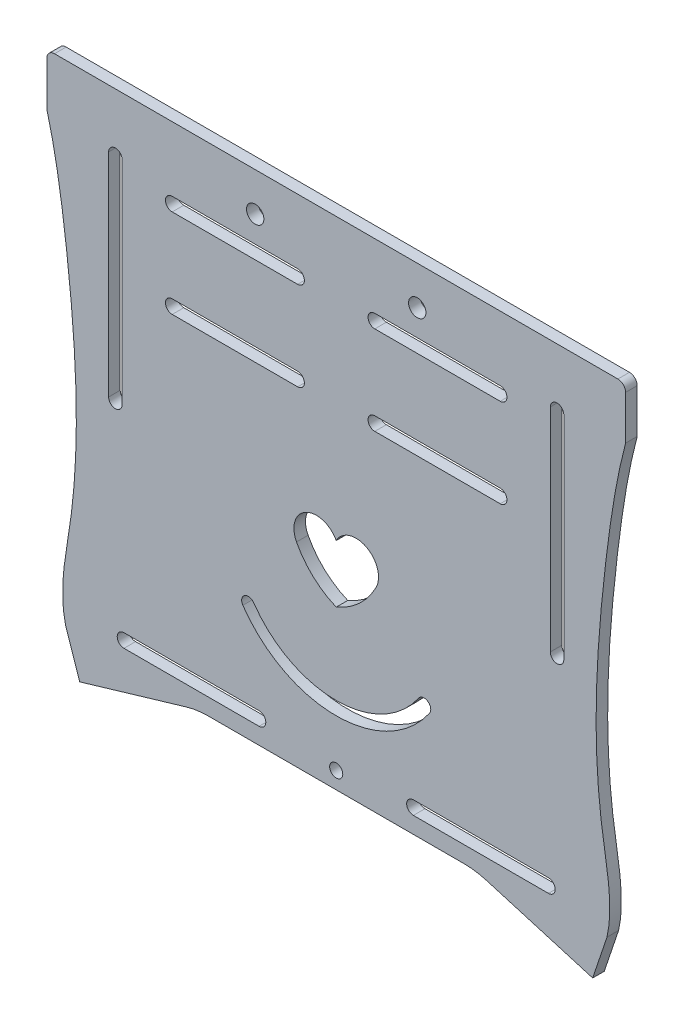
SolidWorks part; units mm, degrees
ref_plane "前视基准面" through (0, 0, 0) normal (0, 0, 1) x (1, 0, 0)
ref_plane "上视基准面" through (0, 0, 0) normal (0, 1, 0) x (1, 0, 0)
ref_plane "右视基准面" through (0, 0, 0) normal (1, 0, 0) x (0, 0, -1)
sketch "草图1" plane through (0, 0, 0) normal (0, 0, 1) x (1, 0, 0)
  line L0 (0, 148.5) -> (0, -94.9538) construction
  line L1 (105, -148.5) -> (-105, -148.5) construction
  line L2 (105, -148.5) -> (105, 148.5) construction
  line L3 (105, 148.5) -> (-105, 148.5) construction
  line L4 (-105, -148.5) -> (-105, 148.5) construction
  line L5 (105, -148.5) -> (-105, 148.5) construction
  line L6 (105, 148.5) -> (-105, -148.5) construction
  line L7 (35.8892, 121.6645) -> (-35.8892, 121.6645)
  line L8 (-35.8892, 121.6645) -> (-66.9017, 102.292)
  line L9 (-75, 40.9339) -> (-75, 31.2613)
  line L10 (-66.9017, 102.292) -> (-66.9017, 52.8701)
  line L11 (75, 40.9339) -> (75, 31.2613)
  line L12 (66.9017, 102.292) -> (66.9017, 52.8701)
  line L13 (35.8892, 121.6645) -> (66.9017, 102.292)
  line L14 (-75, 31.2613) -> (75, 31.2613)
  line L15 (-60, -148.5) -> (-60, -91.8129)
  line L16 (-75, 23.94) -> (75, 23.94)
  line L17 (-75, 23.94) -> (-75, 10.5626)
  line L18 (-38.8455, -105.5906) -> (-66.4608, -113.7617)
  line L19 (-66.4608, -113.7617) -> (-70.1743, -102.7328)
  line L20 (75, 23.94) -> (75, 10.5626)
  line L21 (66.4608, -113.7617) -> (70.1743, -102.7328)
  line L22 (38.8455, -105.5906) -> (66.4608, -113.7617)
  line L23 (-105, 93.0519) -> (105, 93.0519)
  line L24 (-105, 63.0519) -> (105, 63.0519)
  line L25 (-105, -90.0629) -> (-70.5337, -90.0629)
  line L26 (-105, -60.0629) -> (-67.4027, -60.0629)
  line L27 (60, -148.5) -> (60, 148.5)
  line L28 (-60, -58.3129) -> (-45, -58.3129)
  line L29 (-60, -61.8129) -> (-45, -61.8129)
  line L30 (-36, -58.3129) -> (-21, -58.3129)
  line L31 (-36, -61.8129) -> (-21, -61.8129)
  line L32 (-60, -88.3129) -> (-45, -88.3129)
  line L33 (-60, -91.8129) -> (-45, -91.8129)
  line L34 (-36, -88.3129) -> (-21, -88.3129)
  line L35 (-36, -91.8129) -> (-21, -91.8129)
  line L36 (-60, -58.3129) -> (-60, 148.5)
  line L37 (-19.25, -90.0629) -> (105, -90.0629)
  line L38 (-19.25, -60.0629) -> (19.25, -60.0629)
  line L39 (-60, -88.3129) -> (-60, -61.8129)
  line L40 (21, -58.3129) -> (36, -58.3129)
  line L41 (45, -58.3129) -> (60, -58.3129)
  line L42 (60, -61.8129) -> (45, -61.8129)
  line L43 (36, -61.8129) -> (21, -61.8129)
  line L44 (21, -88.3129) -> (36, -88.3129)
  line L45 (21, -91.8129) -> (36, -91.8129)
  line L46 (45, -88.3129) -> (60, -88.3129)
  line L47 (45, -91.8129) -> (60, -91.8129)
  line L48 (37.75, -60.0629) -> (43.25, -60.0629)
  line L49 (58.25, -60.0629) -> (105, -60.0629)
  line L50 (-60, 94.8019) -> (-45, 94.8019)
  line L51 (-36, 94.8019) -> (-21, 94.8019)
  line L52 (-60, 91.3019) -> (-45, 91.3019)
  line L53 (-36, 91.3019) -> (-21, 91.3019)
  line L54 (-60, 64.8019) -> (-45, 64.8019)
  line L55 (-60, 61.3019) -> (-45, 61.3019)
  line L56 (-36, 64.8019) -> (-21, 64.8019)
  line L57 (-36, 61.3019) -> (-21, 61.3019)
  line L58 (21, 94.8019) -> (36, 94.8019)
  line L59 (21, 91.3019) -> (36, 91.3019)
  line L60 (45, 94.8019) -> (60, 94.8019)
  line L61 (45, 91.3019) -> (60, 91.3019)
  line L62 (21, 61.3019) -> (36, 61.3019)
  line L63 (21, 64.8019) -> (36, 64.8019)
  line L64 (45, 61.3019) -> (60, 61.3019)
  line L65 (45, 64.8019) -> (60, 64.8019)
  line L66 (-33.1709, -104.7687) -> (33.1709, -104.7687)
  line L67 (0, -104.7687) -> (0, -148.5) construction
  arc A0 (-75, 40.9339) -> (-66.9017, 52.8701) centre (-79.7474, 52.8701) ccw
  arc A1 (75, 40.9339) -> (66.9017, 52.8701) centre (79.7474, 52.8701) cw
  arc A3 (-60, -88.3129) -> (-60, -91.8129) centre (-60, -90.0629) ccw
  arc A4 (-60, -58.3129) -> (-60, -61.8129) centre (-60, -60.0629) ccw
  circle A5 centre (-60, 63.0519) radius 1.75
  circle A6 centre (-60, 93.0519) radius 1.75
  circle A7 centre (60, 93.0519) radius 1.75
  circle A8 centre (60, 63.0519) radius 1.75
  arc A9 (60, -91.8129) -> (60, -88.3129) centre (60, -90.0629) ccw
  arc A10 (60, -61.8129) -> (60, -58.3129) centre (60, -60.0629) ccw
  arc A11 (-36, -58.3129) -> (-36, -61.8129) centre (-36, -60.0629) ccw
  arc A12 (-36, -88.3129) -> (-36, -91.8129) centre (-36, -90.0629) ccw
  arc A13 (36, -61.8129) -> (36, -58.3129) centre (36, -60.0629) ccw
  arc A14 (36, -91.8129) -> (36, -88.3129) centre (36, -90.0629) ccw
  arc A15 (-45, -61.8129) -> (-45, -58.3129) centre (-45, -60.0629) ccw
  arc A16 (-21, -61.8129) -> (-21, -58.3129) centre (-21, -60.0629) ccw
  arc A17 (-45, -91.8129) -> (-45, -88.3129) centre (-45, -90.0629) ccw
  arc A18 (-21, -91.8129) -> (-21, -88.3129) centre (-21, -90.0629) ccw
  arc A19 (45, -58.3129) -> (45, -61.8129) centre (45, -60.0629) ccw
  arc A20 (21, -58.3129) -> (21, -61.8129) centre (21, -60.0629) ccw
  arc A21 (21, -88.3129) -> (21, -91.8129) centre (21, -90.0629) ccw
  arc A22 (45, -88.3129) -> (45, -91.8129) centre (45, -90.0629) ccw
  circle A23 centre (-36, 93.0519) radius 1.75
  circle A24 centre (-36, 63.0519) radius 1.75
  circle A25 centre (36, 93.0519) radius 1.75
  circle A26 centre (36, 63.0519) radius 1.75
  circle A27 centre (-45, 93.0519) radius 1.75
  circle A28 centre (-21, 93.0519) radius 1.75
  circle A29 centre (-45, 63.0519) radius 1.75
  circle A30 centre (-21, 63.0519) radius 1.75
  circle A31 centre (21, 93.0519) radius 1.75
  circle A32 centre (21, 63.0519) radius 1.75
  circle A33 centre (45, 93.0519) radius 1.75
  circle A34 centre (45, 63.0519) radius 1.75
  arc A35 (33.1709, -104.7687) -> (38.8455, -105.5906) centre (33.1709, -124.7687) cw
  arc A36 (-33.1709, -104.7687) -> (-38.8455, -105.5906) centre (-33.1709, -124.7687) ccw
  spline S0 degree 3 poles (-75, 10.5626) (-72.6959, 1.9073) (-70.3396, -13.3728) (-67.1028, -43.6255) (-66.7657, -72.9327) (-71.8903, -95.1489) (-70.1743, -102.7328) knots 0 0 0 0 0.235247 0.406294 0.801186 1 1 1 1
  spline S1 degree 3 poles (75, 10.5626) (72.6959, 1.9073) (70.3396, -13.3728) (67.1028, -43.6255) (66.7657, -72.9327) (71.8903, -95.1489) (70.1743, -102.7328) knots 0 0 0 0 0.235247 0.406294 0.801186 1 1 1 1
  point P0 (0, 0)
  point P27 (0, 121.6645)
  point P42 (0, -94.0966)
  dimension "D1" = 60
  dimension "D4" = 20
  dimension "D5" = 24
  dimension "D7" = 24
  dimension "D9" = 15
  dimension "D10" = 15
  dimension "D13" = 24
  dimension "D17" = 15
  dimension "D2" = 30
  dimension "D3" = 30
  dimension "D6" = 24
  dimension "D8" = 24
  dimension "D11" = 15
  dimension "D12" = 15
  dimension "D14" = 24
  dimension "D15" = 24
  dimension "D16" = 24
  dimension "D18" = 15
  dimension "D19" = 15
  dimension "D20" = 15
  dimension "D21" = 15
  dimension "D22" = 15
  dimension "D23" = 15
  dimension "D24" = 15
  dimension "D25" = 15
  dimension "D26" = 15
  dimension "D27" = 15
  dimension "D28" = 15
  dimension "D29" = 3.5
  dimension "D30" = 3.5
  dimension "D31" = 3.5
extrude "凸台-拉伸1" add sketch "草图1" along normal blind 3
sketch "草图7" plane through (0, 0, 0) normal (0, 0, -1) x (-1, 0, 0)
  line L0 (0, 121.6645) -> (0, -104.7687) construction
  line L1 (-35.8892, 121.6645) -> (35.8892, 121.6645) construction
  line L2 (33.1709, -104.7687) -> (-33.1709, -104.7687) construction
  line L3 (0, 41.2613) -> (-21, 41.2613) construction
  line L4 (0, 41.2613) -> (21, 41.2613) construction
  line L5 (0, 13.94) -> (-21, 13.94) construction
  line L6 (0, 13.94) -> (21, 13.94) construction
  line L7 (75, 23.94) -> (-75, 23.94) construction
  line L8 (75, 31.2613) -> (-75, 31.2613) construction
  circle A0 centre (-21, 41.2613) radius 1.75
  circle A1 centre (21, 41.2613) radius 1.75
  circle A2 centre (-21, 13.94) radius 2.25
  circle A3 centre (21, 13.94) radius 2.25
  dimension "D1" = 10
  dimension "D2" = 10
extrude "切除-拉伸2" cut sketch "草图7" against normal through all
sketch "草图9" plane through (0, 0, 3) normal (0, 0, 1) x (1, 0, 0)
  line L0 (-70.7828, -98.747) -> (70.7828, -98.747) construction
  line L1 (0, -98.747) -> (0, -104.7687) construction
  line L2 (55, -100.497) -> (20, -100.497)
  line L3 (-55, -96.997) -> (-20, -96.997)
  line L4 (-55, -100.497) -> (-20, -100.497)
  line L5 (-33.1709, -104.7687) -> (33.1709, -104.7687) construction
  line L6 (55, -96.997) -> (20, -96.997)
  arc A0 (-55, -96.997) -> (-55, -100.497) centre (-55, -98.747) ccw
  arc A1 (-20, -100.497) -> (-20, -96.997) centre (-20, -98.747) ccw
  arc A2 (20, -100.497) -> (20, -96.997) centre (20, -98.747) cw
  arc A3 (55, -96.997) -> (55, -100.497) centre (55, -98.747) cw
  spline S0 degree 3 poles (-75, 10.5626) (-72.6959, 1.9073) (-70.3396, -13.3728) (-67.1028, -43.6255) (-66.7657, -72.9327) (-71.8903, -95.1489) (-70.1743, -102.7328) knots 0 0 0 0 0.235247 0.406294 0.801186 1 1 1 1 construction
  spline S1 degree 3 poles (75, 10.5626) (72.6959, 1.9073) (70.3396, -13.3728) (67.1028, -43.6255) (66.7657, -72.9327) (71.8903, -95.1489) (70.1743, -102.7328) knots 0 0 0 0 0.235247 0.406294 0.801186 1 1 1 1 construction
  dimension "D1" = 35
  dimension "D2" = 20
extrude "切除-拉伸4" cut sketch "草图9" against normal blind 3
sketch "草图10" plane through (0, 0, 3) normal (0, 0, 1) x (1, 0, 0)
  line L0 (-21, -60.0629) -> (-21, -90.0629) construction
  line L1 (21, -60.0629) -> (21, -90.0629) construction
  line L2 (-21, -75.0629) -> (-17.5, -75.0629) construction
  line L4 (12.5, -80.0629) -> (-12.5, -80.0629)
  line L6 (12.5, -70.0629) -> (-12.5, -70.0629)
  line L11 (17.5, -75.0629) -> (21, -75.0629) construction
  arc A0 (-12.5, -70.0629) -> (-12.5, -80.0629) centre (-12.5, -75.0629) ccw
  arc A1 (12.5, -80.0629) -> (12.5, -70.0629) centre (12.5, -75.0629) ccw
  point P11 (0, -75.0629)
extrude "切除-拉伸5" cut sketch "草图10" against normal blind 3
sketch "草图11" plane through (0, 0, 3) normal (0, 0, 1) x (1, 0, 0)
  line L0 (-21, 93.0519) -> (-21, 63.0519) construction
  line L1 (21, 93.0519) -> (21, 63.0519) construction
  line L2 (-21, 78.0519) -> (-20, 78.0519) construction
  line L4 (15, 73.0519) -> (-15, 73.0519)
  line L6 (15, 83.0519) -> (-15, 83.0519)
  line L10 (20, 78.0519) -> (21, 78.0519) construction
  arc A0 (-15, 83.0519) -> (-15, 73.0519) centre (-15, 78.0519) ccw
  arc A1 (15, 73.0519) -> (15, 83.0519) centre (15, 78.0519) ccw
  point P10 (0, 78.0519)
  dimension "D1" = 30
extrude "切除-拉伸8" cut sketch "草图11" against normal blind 3
sketch "草图12" plane through (0, 0, 3) normal (0, 0, 1) x (1, 0, 0)
  line L0 (0, 121.6645) -> (0, 83.0519) construction
  line L1 (35.8892, 121.6645) -> (-35.8892, 121.6645) construction
  line L2 (15, 83.0519) -> (-15, 83.0519) construction
  circle A0 centre (0, 106.3718) radius 11 construction
  circle A1 centre (0, 106.3718) radius 8 construction
  circle A2 centre (0, 114.3718) radius 1.7
  circle A3 centre (0, 98.3718) radius 1.7
  circle A4 centre (8, 106.3718) radius 1.7
  circle A5 centre (-8, 106.3718) radius 1.7
extrude "切除-拉伸9" cut sketch "草图12" against normal blind 3
sketch "草图13" plane through (0, 0, 3) normal (0, 0, 1) x (1, 0, 0)
  line L0 (0, -104.7687) -> (0, -80.0629) construction
  line L1 (-33.1709, -104.7687) -> (33.1709, -104.7687) construction
  line L2 (-12.5, -80.0629) -> (12.5, -80.0629) construction
  circle A0 centre (0, -92.4158) radius 8 construction
  circle A1 centre (0, -84.4158) radius 1.7
  circle A2 centre (8, -92.4158) radius 1.7
  circle A3 centre (0, -100.4158) radius 1.7
  circle A4 centre (-8, -92.4158) radius 1.7
extrude "切除-拉伸11" cut sketch "草图13" against normal blind 3
sketch "草图14" plane through (0, 0, 3) normal (0, 0, 1) x (1, 0, 0)
  line L0 (0, 23.94) -> (0, -104.7687) construction
  line L1 (-55.4755, 8.9197) -> (-55.4755, -46.0803)
  line L2 (-58.9755, 8.9197) -> (-58.9755, -46.0803)
  line L3 (-75, 23.94) -> (75, 23.94) construction
  line L4 (-33.1709, -104.7687) -> (33.1709, -104.7687) construction
  line L5 (58.9755, 8.9197) -> (58.9755, -46.0803)
  line L6 (55.4755, 8.9197) -> (55.4755, -46.0803)
  arc A0 (-55.4755, 8.9197) -> (-58.9755, 8.9197) centre (-57.2255, 8.9197) ccw
  arc A1 (-58.9755, -46.0803) -> (-55.4755, -46.0803) centre (-57.2255, -46.0803) ccw
  arc A2 (58.9755, -46.0803) -> (55.4755, -46.0803) centre (57.2255, -46.0803) cw
  arc A3 (55.4755, 8.9197) -> (58.9755, 8.9197) centre (57.2255, 8.9197) cw
extrude "切除-拉伸12" cut sketch "草图14" against normal through all
fillet "圆角1" radius 2 2 edges at (75, 31.2613, 1.5) (-75, 31.2613, 1.5)
fillet "圆角2" radius 2 2 edges at (-75, 23.94, 1.5) (75, 23.94, 1.5)
sketch "草图15" plane through (0, 0, 0) normal (0, 0, -1) x (-1, 0, 0)
  line L0 (0, 121.6645) -> (0, 31.2613) construction
  line L1 (-35.8892, 121.6645) -> (35.8892, 121.6645) construction
  line L2 (73, 31.2613) -> (-73, 31.2613) construction
  line L3 (-27.5188, 121.6645) -> (-63.6963, 99.0657) construction
  line L4 (-35.8892, 121.6645) -> (-66.9017, 102.292) construction
  line L5 (-61.1842, 102.4035) -> (-34.7748, 118.9006)
  line L6 (-59.5948, 99.8591) -> (-33.1854, 116.3562)
  line L7 (27.5188, 121.6645) -> (63.6963, 99.0657) construction
  line L8 (59.5948, 99.8591) -> (33.1854, 116.3562)
  line L9 (61.1842, 102.4035) -> (34.7748, 118.9006)
  arc A0 (-61.1842, 102.4035) -> (-59.5948, 99.8591) centre (-60.3895, 101.1313) ccw
  arc A1 (-33.1854, 116.3562) -> (-34.7748, 118.9006) centre (-33.9801, 117.6284) ccw
  arc A2 (33.1854, 116.3562) -> (34.7748, 118.9006) centre (33.9801, 117.6284) cw
  arc A3 (61.1842, 102.4035) -> (59.5948, 99.8591) centre (60.3895, 101.1313) cw
extrude "切除-拉伸13" cut sketch "草图15" against normal through all
sketch "草图16" plane through (0, 0, 0) normal (0, 0, -1) x (-1, 0, 0)
  line L0 (0, 121.6645) -> (0, 31.2613) construction
  line L1 (-35.8892, 121.6645) -> (35.8892, 121.6645) construction
  line L2 (73, 31.2613) -> (-73, 31.2613) construction
  line L3 (-21, 41.2613) -> (-66.71, 41.2613) construction
  line L4 (-62, 43.0113) -> (-32, 43.0113)
  line L5 (-62, 39.5113) -> (-32, 39.5113)
  line L6 (21, 41.2613) -> (66.71, 41.2613) construction
  line L7 (62, 39.5113) -> (32, 39.5113)
  line L8 (62, 43.0113) -> (32, 43.0113)
  line L9 (-75, 40.9339) -> (-75, 33.2613) construction
  arc A0 (-62, 43.0113) -> (-62, 39.5113) centre (-62, 41.2613) ccw
  arc A1 (-32, 39.5113) -> (-32, 43.0113) centre (-32, 41.2613) ccw
  arc A2 (32, 39.5113) -> (32, 43.0113) centre (32, 41.2613) cw
  arc A3 (62, 43.0113) -> (62, 39.5113) centre (62, 41.2613) cw
  dimension "D2" = 13
sketch "草图17" plane through (0, 0, 0) normal (0, 0, -1) x (-1, 0, 0)
  text T0 "Y" font "黑体" height in points 72
extrude "切除-拉伸15" cut sketch "草图17" against normal through all
sketch "草图18" plane through (0, 0, 0) normal (0, 0, -1) x (-1, 0, 0)
  text T0 "H" font "黑体" height in points 72
extrude "切除-拉伸16" cut sketch "草图18" against normal through all
sketch "草图20" plane through (0, 0, 0) normal (0, 0, -1) x (-1, 0, 0)
  line L0 (-66.9017, 102.292) -> (-66.9017, 52.8701) construction
  line L1 (-66.9017, 95.8596) -> (66.9017, 95.8596)
  line L2 (-66.9017, 95.8596) -> (-66.9017, 52.8701)
  line L3 (-66.9017, 52.8701) -> (66.9017, 52.8701)
  line L4 (66.9017, 95.8596) -> (66.9017, 52.8701)
extrude "凸台-拉伸2" add sketch "草图20" against normal blind 3
sketch "草图21" plane through (0, 0, 0) normal (0, 0, -1) x (-1, 0, 0)
  line L1 (-64.7663, -56.4228) -> (64.4409, -56.4228)
  line L2 (-64.7663, -56.4228) -> (-64.7663, -95.2117)
  line L3 (-64.7663, -95.2117) -> (64.4409, -95.2117)
  line L4 (64.4409, -56.4228) -> (64.4409, -95.2117)
extrude "凸台-拉伸3" add sketch "草图21" against normal blind 3
sketch "草图22" plane through (0, 0, 0) normal (0, 0, -1) x (-1, 0, 0)
  line L1 (-46.7188, -3.1128) -> (-25.8503, -3.1128)
  line L2 (-46.7188, -3.1128) -> (-46.7188, -34.3233)
  line L3 (-46.7188, -34.3233) -> (-25.8503, -34.3233)
  line L4 (-25.8503, -3.1128) -> (-25.8503, -34.3233)
  line L5 (28.8143, -3.1128) -> (49.8675, -3.1128)
  line L6 (28.8143, -3.1128) -> (28.8143, -33.2152)
  line L7 (28.8143, -33.2152) -> (49.8675, -33.2152)
  line L8 (49.8675, -3.1128) -> (49.8675, -33.2152)
extrude "凸台-拉伸4" add sketch "草图22" against normal blind 3
sketch "草图24" plane through (0, 0, 0) normal (0, 0, -1) x (-1, 0, 0)
  line L1 (-64.9961, 44.3276) -> (-28.6954, 44.3276)
  line L2 (-64.9961, 44.3276) -> (-64.9961, 38.3743)
  line L3 (-64.9961, 38.3743) -> (-28.6954, 38.3743)
  line L4 (-28.6954, 44.3276) -> (-28.6954, 38.3743)
  line L5 (29.2405, 44.3276) -> (65.8315, 44.3276)
  line L6 (29.2405, 44.3276) -> (29.2405, 38.3743)
  line L7 (29.2405, 38.3743) -> (65.8315, 38.3743)
  line L8 (65.8315, 44.3276) -> (65.8315, 38.3743)
extrude "凸台-拉伸5" add sketch "草图24" against normal blind 3
sketch "草图25" plane through (0, 0, 0) normal (0, 0, -1) x (-1, 0, 0)
  line L0 (-32.6582, 113.0113) -> (-14.6582, 113.0113)
  line L1 (-32.6582, 109.5113) -> (-14.6582, 109.5113)
  line L2 (-21, 41.2613) -> (21, 41.2613)
  line L3 (-0.3165, 111.2613) -> (0, 41.2613) construction
  line L4 (14.3418, 113.0113) -> (32.3418, 113.0113)
  line L5 (32.3418, 41.2613) -> (-32.6582, 41.2613)
  line L6 (32.3418, 41.2613) -> (32.3418, 111.2613)
  line L8 (-32.6582, 41.2613) -> (-32.6582, 111.2613)
  line L9 (32.3418, 41.2613) -> (-32.6582, 111.2613) construction
  line L10 (30.7168, 109.5113) -> (-32.6582, 41.2613) construction
  line L11 (14.3418, 109.5113) -> (32.3418, 109.5113)
  line L12 (32.3418, 76.2613) -> (-32.6582, 76.2613) construction
  line L13 (12.5918, 111.2613) -> (-12.9082, 111.2613)
  line L14 (12.5918, 41.2613) -> (-12.9082, 41.2613)
  line L15 (14.3418, 43.0113) -> (32.3418, 43.0113)
  line L16 (14.3418, 39.5113) -> (32.3418, 39.5113)
  line L17 (-32.6582, 43.0113) -> (-14.6582, 43.0113)
  line L18 (-32.6582, 39.5113) -> (-14.6582, 39.5113)
  circle A0 centre (-32.6582, 111.2613) radius 1.75
  arc A1 (32.3418, 109.5113) -> (32.3418, 113.0113) centre (32.3418, 111.2613) ccw
  arc A2 (-14.6582, 109.5113) -> (-14.6582, 113.0113) centre (-14.6582, 111.2613) ccw
  arc A3 (14.3418, 113.0113) -> (14.3418, 109.5113) centre (14.3418, 111.2613) ccw
  arc A4 (14.3418, 39.5113) -> (14.3418, 43.0113) centre (14.3418, 41.2613) cw
  arc A5 (-14.6582, 43.0113) -> (-14.6582, 39.5113) centre (-14.6582, 41.2613) cw
  arc A6 (32.3418, 43.0113) -> (32.3418, 39.5113) centre (32.3418, 41.2613) cw
  circle A7 centre (-32.6582, 41.2613) radius 1.75
  point P9 (-0.1582, 76.2613)
  dimension "D1" = 18
  dimension "D2" = 18
extrude "切除-拉伸17" cut sketch "草图25" against normal through all
extrude "切除-拉伸19" cut sketch "草图16" against normal through all
sketch "草图26" plane through (0, 0, 0) normal (0, 0, -1) x (-1, 0, 0)
  line L0 (0, 121.6645) -> (0, -104.7687) construction
  line L1 (-35.8892, 121.6645) -> (35.8892, 121.6645) construction
  line L2 (33.1709, -104.7687) -> (-33.1709, -104.7687) construction
  line L4 (15, 71.877) -> (-15, 71.877)
  line L6 (15, 81.877) -> (-15, 81.877)
  arc A0 (-15, 81.877) -> (-15, 71.877) centre (-15, 76.877) ccw
  arc A1 (15, 71.877) -> (15, 81.877) centre (15, 76.877) ccw
  point P6 (0, 76.877)
extrude "切除-拉伸20" cut sketch "草图26" against normal through all
sketch "草图27" plane through (0, 0, 0) normal (0, 0, -1) x (-1, 0, 0)
  line L0 (0, 23.94) -> (0, -104.7687) construction
  line L1 (73, 23.94) -> (-73, 23.94) construction
  line L2 (33.1709, -104.7687) -> (-33.1709, -104.7687) construction
  line L3 (-42.5, -15.81) -> (-10, -15.81)
  line L4 (42.5, -17.56) -> (-42.5, -17.56)
  line L5 (42.5, -17.56) -> (42.5, 5.44)
  line L6 (42.5, 5.44) -> (-42.5, 5.44)
  line L7 (-42.5, -17.56) -> (-42.5, 5.44)
  line L8 (42.5, -17.56) -> (-42.5, 5.44) construction
  line L9 (42.5, 5.44) -> (-42.5, -17.56) construction
  line L10 (-42.5, -19.31) -> (-10, -19.31)
  line L11 (-42.5, 7.19) -> (-10, 7.19)
  line L12 (-42.5, 3.69) -> (-10, 3.69)
  line L13 (10, 7.19) -> (42.5, 7.19)
  line L14 (10, 3.69) -> (42.5, 3.69)
  line L15 (10, -15.81) -> (42.5, -15.81)
  line L16 (10, -19.31) -> (42.5, -19.31)
  circle A0 centre (-42.5, 5.44) radius 1.75
  circle A1 centre (-42.5, -17.56) radius 1.75
  circle A2 centre (42.5, 5.44) radius 1.75
  circle A3 centre (42.5, -17.56) radius 1.75
  circle A4 centre (-10, 5.44) radius 1.75
  circle A5 centre (-10, -17.56) radius 1.75
  circle A6 centre (10, -17.56) radius 1.75
  circle A7 centre (10, 5.44) radius 1.75
  point P6 (0, -6.06)
  dimension "D4" = 10
  dimension "D5" = 10
  dimension "D1" = 30
  dimension "D2" = 85
  dimension "D3" = 23
extrude "切除-拉伸21" cut sketch "草图27" against normal through all contours L6 A0 L7 | L7 A0 L6 | A4 L11 A0 L6 | A4 L6 A0 L12 | L6 A4 | L6 A4 | A7 L6 | A7 L6 | L6 A7 L14 A2 | L13 A7 L6 A2 | A2 L6 L5 | L6 A2 L5 | L7 A1 L4 | L4 A1 L7 | A5 L3 A1 L4 | A5 L4 A1 L10 | L4 A5 | L4 A5 | A6 L4 | A6 L4 | L4 A6 L16 A3 | L15 A6 L4 A3 | L4 A3 L5 | L5 A3 L4
sketch "草图28" plane through (0, 0, 0) normal (0, 0, -1) x (-1, 0, 0)
  line L0 (0, 23.94) -> (0, -104.7687) construction
  line L1 (73, 23.94) -> (-73, 23.94) construction
  line L2 (33.1709, -104.7687) -> (-33.1709, -104.7687) construction
  arc A0 (0, -48.8123) -> (-10.2848, -54.2659) centre (-5.1424, -51.5391) ccw
  arc A1 (-10.2848, -54.2659) -> (0, -63.7557) centre (7.9187, -44.8556) ccw
  arc A2 (10.2848, -54.2659) -> (0, -63.7557) centre (-7.9187, -44.8556) cw
  arc A3 (0, -48.8123) -> (10.2848, -54.2659) centre (5.1424, -51.5391) cw
extrude "切除-拉伸22" cut sketch "草图28" against normal through all
sketch "草图29" plane through (0, 0, 0) normal (0, 0, -1) x (-1, 0, 0)
  line L0 (0, 23.94) -> (0, -104.7687) construction
  line L1 (73, 23.94) -> (-73, 23.94) construction
  line L2 (33.1709, -104.7687) -> (-33.1709, -104.7687) construction
  arc A0 (-21.3687, -73.4908) -> (21.3687, -73.4908) centre (0, -58.7579) ccw
  arc A1 (-24.1996, -75.4426) -> (24.1996, -75.4426) centre (0, -58.7579) ccw
  arc A2 (-21.3687, -73.4908) -> (-24.1996, -75.4426) centre (-22.7842, -74.4667) ccw
  arc A3 (24.1996, -75.4426) -> (21.3687, -73.4908) centre (22.7842, -74.4667) ccw
extrude "切除-拉伸23" cut sketch "草图29" against normal blind 3
sketch "草图30" plane through (0, 0, 0) normal (0, 0, -1) x (-1, 0, 0)
  line L1 (-105.3936, 135.3537) -> (91.9343, 135.3537)
  line L2 (-105.3936, 135.3537) -> (-105.3936, 25.56)
  line L3 (-105.3936, 25.56) -> (91.9343, 25.56)
  line L4 (91.9343, 135.3537) -> (91.9343, 25.56)
extrude "切除-拉伸24" cut sketch "草图30" against normal blind 10
